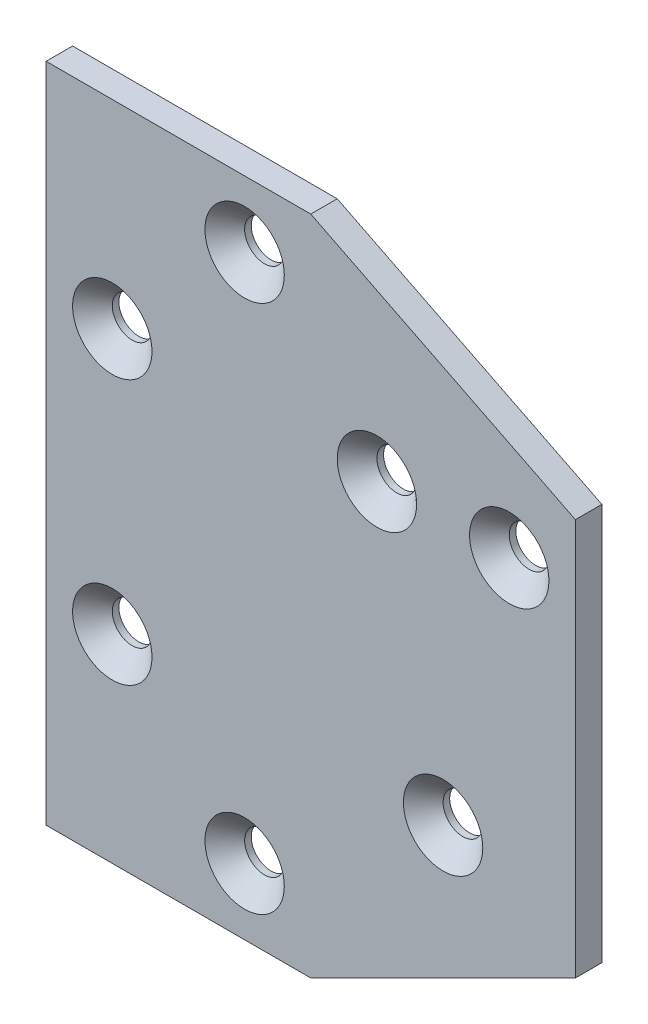
SolidWorks part; units mm, degrees
ref_plane "Front Plane" through (0, 0, 0) normal (0, 0, 1) x (1, 0, 0)
ref_plane "Top Plane" through (0, 0, 0) normal (0, 1, 0) x (1, 0, 0)
ref_plane "Right Plane" through (0, 0, 0) normal (1, 0, 0) x (0, 0, -1)
sketch "Sketch1" plane through (0, 0, 0) normal (0, 0, 1) x (1, 0, 0)
  line L0 (20, 50) -> (60, 30)
  line L1 (-20, -50) -> (20, -50)
  line L2 (-20, -50) -> (-20, 50)
  line L3 (-20, 50) -> (20, 50)
  line L4 (20, -50) -> (20, 50)
  line L5 (-20, -50) -> (20, 50) construction
  line L6 (-20, 50) -> (20, -50) construction
  line L7 (60, -30) -> (20, -30)
  line L8 (60, -30) -> (60, 30)
  line L9 (60, 30) -> (20, 30)
  line L10 (20, -30) -> (20, 30)
  line L11 (60, -30) -> (20, 30) construction
  line L12 (60, 30) -> (20, -30) construction
  line L13 (20, -50) -> (60, -30)
  line L14 (0, 0) -> (40, 0) construction
  point P0 (0, 0)
  point P9 (40, 0)
  dimension "D1" = 60
  dimension "D2" = 40
  dimension "D3" = 40
  dimension "D4" = 100
extrude "Boss-Extrude1" add sketch "Sketch1" along normal mid plane 4 contours L1 L4 L3 L2 | L9 L0 L4 | L8 L9 L4 L7 | L4 L13 L7
sketch "Sketch2" plane through (0, 0, 2) normal (0, 0, 1) x (1, 0, 0)
  line L0 (-10, 20) -> (-10, -20) construction
  line L1 (-10, -20) -> (40, -20) construction
  line L2 (10, -40) -> (10, 40) construction
  line L3 (30, 20) -> (50, 20) construction
  line L4 (-10, 20) -> (30, 20) construction
  circle A0 centre (-10, 20) radius 3
  circle A2 centre (-10, -20) radius 3
  circle A3 centre (10, -40) radius 3
  circle A4 centre (40, -20) radius 3
  circle A5 centre (30, 20) radius 3
  circle A6 centre (50, 20) radius 3
  circle A7 centre (10, 40) radius 3
  point P15 (0, 0)
  dimension "D8" = 6
  dimension "D1" = 20
  dimension "D2" = 10
  dimension "D3" = 20
  dimension "D4" = 20
  dimension "D5" = 20
  dimension "D6" = 40
  dimension "D7" = 20
  dimension "D9" = 10
extrude "Cut-Extrude1" cut sketch "Sketch2" against normal through all
chamfer "Chamfer1" distance 3 angle 45 7 edges at (13, -40, 2) (43, -20, 2) (-7, -20, 2) (53, 20, 2) (33, 20, 2) (13, 40, 2) (-7, 20, 2)
fillet "Fillet1" [suppressed] radius 1
